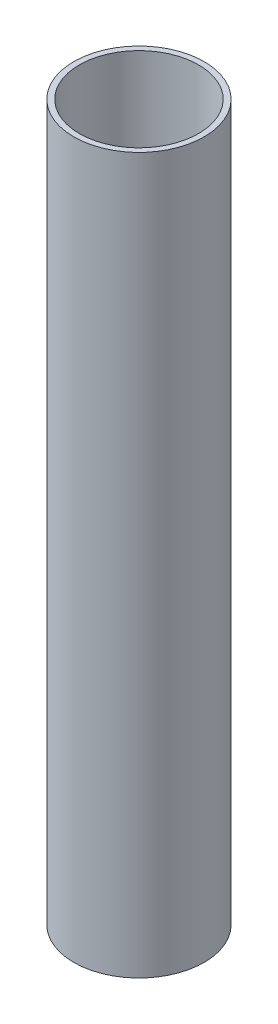
SolidWorks part; units mm, degrees
material "C-Glass Fiber"
ref_plane "Front Plane" through (0, 0, 0) normal (0, 0, 1) x (1, 0, 0)
ref_plane "Top Plane" through (0, 0, 0) normal (0, 1, 0) x (1, 0, 0)
ref_plane "Right Plane" through (0, 0, 0) normal (1, 0, 0) x (0, 0, -1)
sketch "Sketch1" plane through (0, 0, 0) normal (0, 1, 0) x (1, 0, 0)
  circle A0 centre (0, 0) radius 38.1
  circle A1 centre (0, 0) radius 41.6814
  dimension "D1" = 3.5814
  dimension "D2" = 76.2
extrude "Boss-Extrude1" add sketch "Sketch1" along normal blind 457.2
